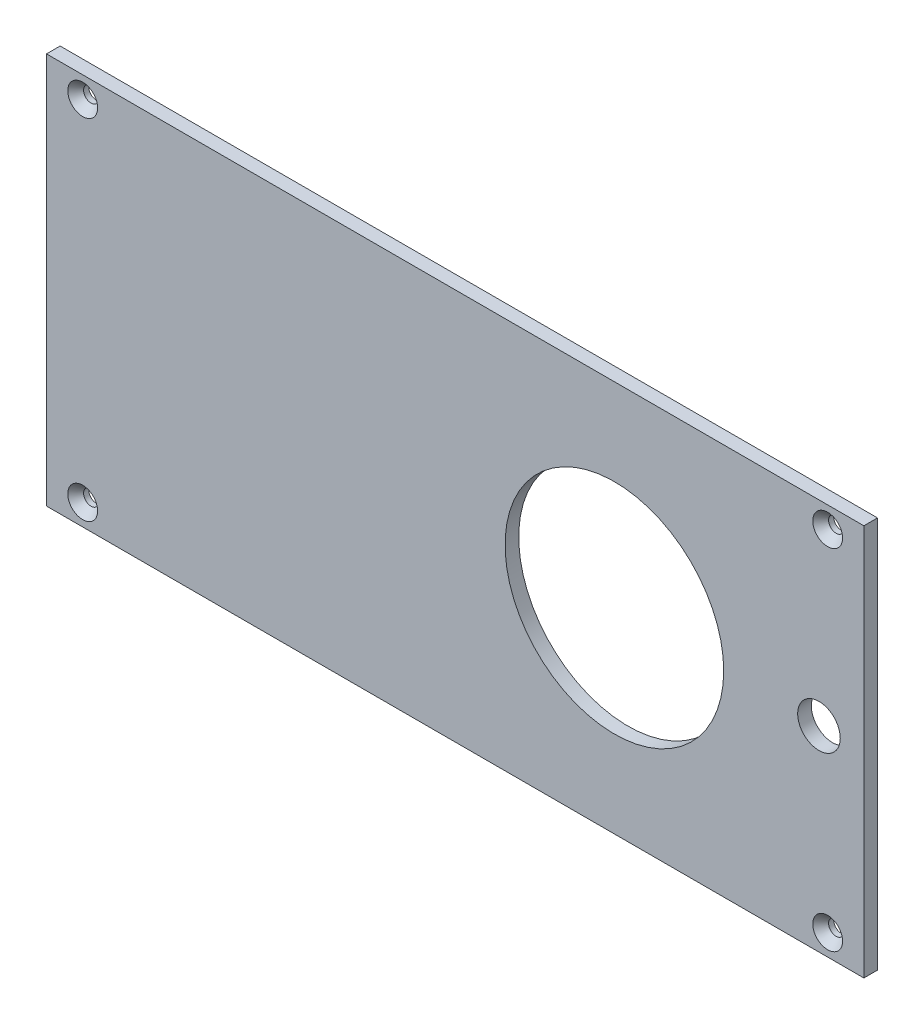
SolidWorks part; units mm, degrees
material "6061-T4 (SS)"
ref_plane "Front Plane" through (0, 0, 0) normal (0, 0, 1) x (1, 0, 0)
ref_plane "Top Plane" through (0, 0, 0) normal (0, 1, 0) x (1, 0, 0)
ref_plane "Right Plane" through (0, 0, 0) normal (1, 0, 0) x (0, 0, -1)
sketch "Sketch1" plane through (0, 0, 0) normal (0, 0, 1) x (1, 0, 0)
  line L1 (0, 0) -> (96, 0)
  line L2 (0, 0) -> (0, 46)
  line L3 (0, 46) -> (96, 46)
  line L4 (96, 0) -> (96, 46)
  dimension "D1" = 46
  dimension "D2" = 96
extrude "Boss-Extrude1" add sketch "Sketch1" along normal blind 1.6002
sketch "Sketch2" plane through (0, 0, 1.6002) normal (0, 0, 1) x (1, 0, 0)
  circle A0 centre (66.7, 23) radius 12.8397
  circle A5 centre (66.7, 23) radius 12.7 construction
  dimension "D1" = 25.6794
extrude "Cut-Extrude1" cut sketch "Sketch2" against normal through all
hole_wizard "CSK for #0 Flat Head Socket Cap Screw1" positions "Sketch6" profile "Sketch7" countersink size "#0" standard "ANSI Inch" end condition through all
sketch "Sketch6" plane through (0, 0, 1.6002) normal (0, 0, 1) x (1, 0, 0)
  line L0 (0, 46) -> (0, 0) construction
  line L1 (4.25, 43.5) -> (4.25, 2.5) construction
  line L2 (4.25, 2.5) -> (91.75, 2.5) construction
  line L3 (91.75, 2.5) -> (91.75, 43.5) construction
  line L4 (91.75, 43.5) -> (4.25, 43.5) construction
  line L6 (96, 0) -> (96, 46) construction
  line L8 (96, 46) -> (0, 46) construction
  line L9 (0, 0) -> (96, 0) construction
  point P0 (4.25, 43.5)
  point P2 (4.25, 2.5)
  point P4 (91.75, 2.5)
  point P6 (91.75, 43.5)
  dimension "D1" = 4.25
  dimension "D2" = 4.25
  dimension "D3" = 2.5
  dimension "D4" = 2.5
sketch "Sketch7" plane through (4.25, 43.5, 1.6002) normal (1, 0, 0) x (0, -1, 0)
  line L0 (0, 0) -> (0, 1.6002)
  line L1 (0, 1.6002) -> (0.889, 1.6002)
  line L2 (0.889, 1.6002) -> (0.889, 0.9935)
  line L3 (0.889, 0.9935) -> (1.7526, 0)
  line L5 (1.7526, 0) -> (0, 0)
  line L6 (-0.889, 0.9935) -> (-1.7526, 0) construction
  line L11 (0, -6.35) -> (0, 107.95) construction
  dimension "Thru Hole Dia." = 1.778
  dimension "Thru Hole Depth" = 1.6002
  dimension "Near C'Sink Dia." = 3.5052
  dimension "Near C'Sink Angle" = 82
sketch "Sketch14" plane through (0, 0, 1.6002) normal (0, 0, 1) x (1, 0, 0)
  circle A0 centre (90.727, 23) radius 2.5
  circle A1 centre (90.727, 23) radius 1.2192 construction
  dimension "D1" = 5
extrude "Cut-Extrude2" cut sketch "Sketch14" against normal blind 10 contours A0
